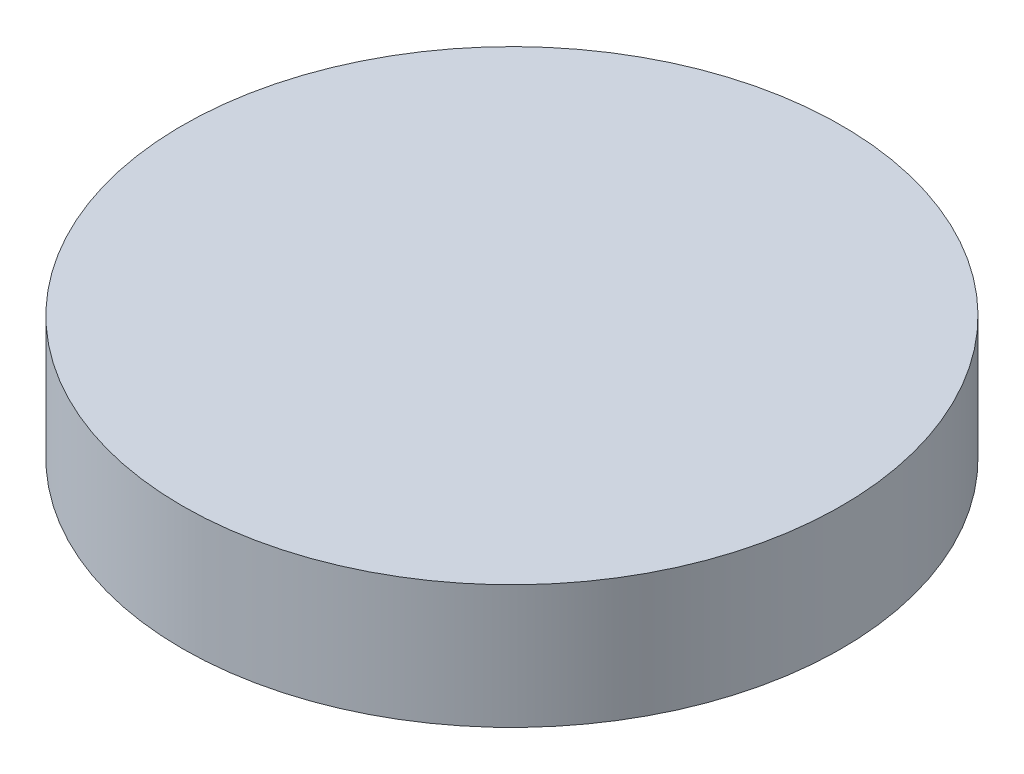
SolidWorks part; units mm, degrees
ref_plane "Front Plane" through (0, 0, 0) normal (0, 0, 1) x (1, 0, 0)
ref_plane "Top Plane" through (0, 0, 0) normal (0, 1, 0) x (1, 0, 0)
ref_plane "Right Plane" through (0, 0, 0) normal (1, 0, 0) x (0, 0, -1)
sketch "Sketch1" plane through (0, 0, 0) normal (0, 1, 0) x (1, 0, 0)
  circle A0 centre (0, 0) radius 40
  dimension "D1" = 80
extrude "Boss-Extrude1" add sketch "Sketch1" along normal blind 15
